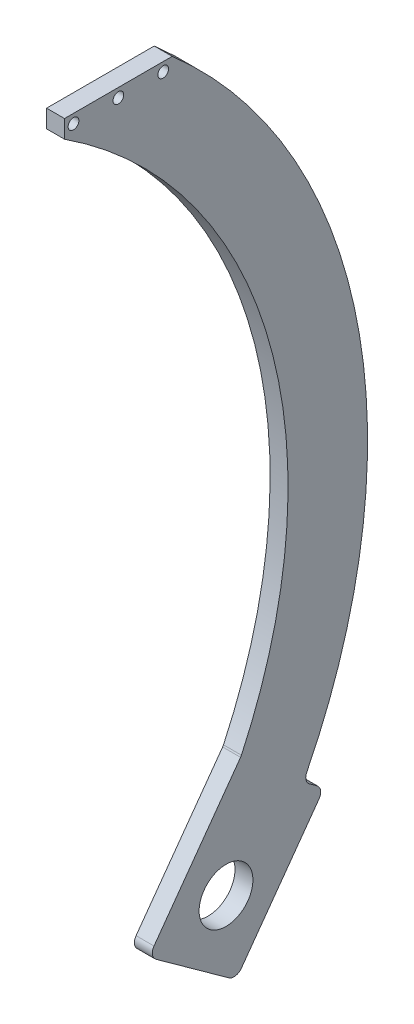
SolidWorks part; units mm, degrees
material "6061-T6 (SS)"
ref_plane "Front Plane" through (0, 0, 0) normal (0, 0, 1) x (1, 0, 0)
ref_plane "Top Plane" through (0, 0, 0) normal (0, 1, 0) x (1, 0, 0)
ref_plane "Right Plane" through (0, 0, 0) normal (1, 0, 0) x (0, 0, -1)
sketch "Sketch1" plane through (0, 0, 0) normal (1, 0, 0) x (0, 0, -1)
  line L0 (0, 266.7) -> (0, -149.8368) construction
  line L1 (0, 0) -> (38.1, 0) construction
  line L2 (-19.05, 266.7) -> (19.05, 266.7)
  line L3 (-19.05, 266.7) -> (-19.05, 260.35)
  line L4 (76.2, 52.8631) -> (0, -52.8631) construction
  line L8 (41.6734, -27.6231) -> (72.861, 15.6492)
  line L9 (16.7086, -9.6302) -> (72.861, 15.6492) construction
  line L10 (41.9522, 37.926) -> (35.7294, -23.3391) construction
  line L11 (10.7646, -5.3462) -> (41.6734, -27.6231)
  line L12 (10.7646, -5.3462) -> (41.9522, 37.926)
  line L13 (65.4323, 21.0032) -> (72.861, 15.6492)
  line L14 (41.9522, 37.926) -> (43.4338, 39.9816)
  arc A0 (0, 266.7) -> (0, -38.1) centre (-114.3, 114.3) cw construction
  arc A1 (-19.05, 260.35) -> (43.4338, 39.9816) centre (-114.3, 114.3) cw
  arc A2 (19.05, 266.7) -> (65.4323, 21.0032) centre (-114.3, 114.3) cw
  circle A3 centre (38.1, 0) radius 9.525
  point P10 (0, 266.7)
  point P19 (38.1, 0)
  dimension "D3" = 190.5
  dimension "D5" = 6.35
  dimension "D6" = 19.05
  dimension "D1" = 38.1
  dimension "D2" = 266.7
  dimension "D4" = 38.1
  dimension "D7" = 38.1
  dimension "D8" = 2.5339
  dimension "D9" = 20.32
  dimension "D10" = 19.05
  dimension "D11" = 9.1571
extrude "Boss-Extrude1" add sketch "Sketch1" along normal blind 6.35 contours A1 L14 L12 L11 L8 L13 A2 L2 L3 | A3
fillet "Fillet1" radius 3.175 5 edges at (3.175, 39.9816, -43.4338) (3.175, 21.0032, -65.4323) (3.175, 15.6492, -72.861) (3.175, -27.6231, -41.6734) (3.175, -5.3462, -10.7646)
hole_wizard "#6 Clearance Hole1" positions "Sketch2" profile "Sketch3" hole size "#6" standard "ANSI Inch" end condition up to next
sketch "Sketch2" plane through (6.35, 0, 0) normal (1, 0, 0) x (0, 0, -1)
  line L0 (-19.05, 266.7) -> (-19.05, 260.35) construction
  line L1 (-19.05, 266.7) -> (19.05, 266.7) construction
  point P0 (-15.875, 263.525)
  point P2 (15.875, 263.525)
  point P4 (0, 263.525)
  dimension "D1" = 31.75
  dimension "D2" = 3.175
  dimension "D3" = 3.175
  dimension "D4" = 15.875
sketch "Sketch3" plane through (6.35, 263.525, 15.875) normal (0, 1, 0) x (0, 0, -1)
  line L0 (0, 0) -> (0, 6.35)
  line L1 (0, 6.35) -> (1.8986, 6.35)
  line L2 (1.8986, 6.35) -> (1.8986, 0)
  line L5 (1.8986, 0) -> (0, 0)
  line L11 (0, -6.35) -> (0, 107.95) construction
  dimension "Thru Hole Dia." = 3.7973
  dimension "Thru Hole Depth" = 6.35
